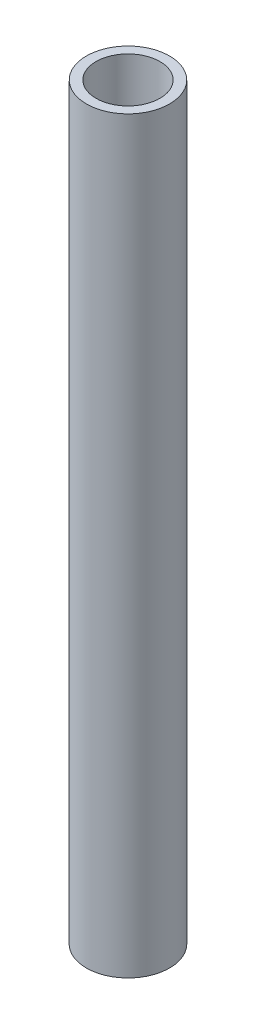
SolidWorks part; units mm, degrees
material "AISI 4130 Steel, annealed at 865C"
ref_plane "X-Y Datum" through (0, 0, 0) normal (0, 0, 1) x (1, 0, 0)
ref_plane "X-Z Datum" through (0, 0, 0) normal (0, 1, 0) x (1, 0, 0)
ref_plane "Y-Z Datum" through (0, 0, 0) normal (1, 0, 0) x (0, 0, -1)
sketch "Sketch1" plane through (0, 0, 0) normal (0, 1, 0) x (1, 0, 0)
  circle A0 centre (0, 0) radius 6.35
  circle A1 centre (0, 0) radius 4.8768
  dimension "D1" = 12.7
  dimension "D2" = 1.4732
extrude "Boss-Extrude1" add sketch "Sketch1" along normal blind 114.3
